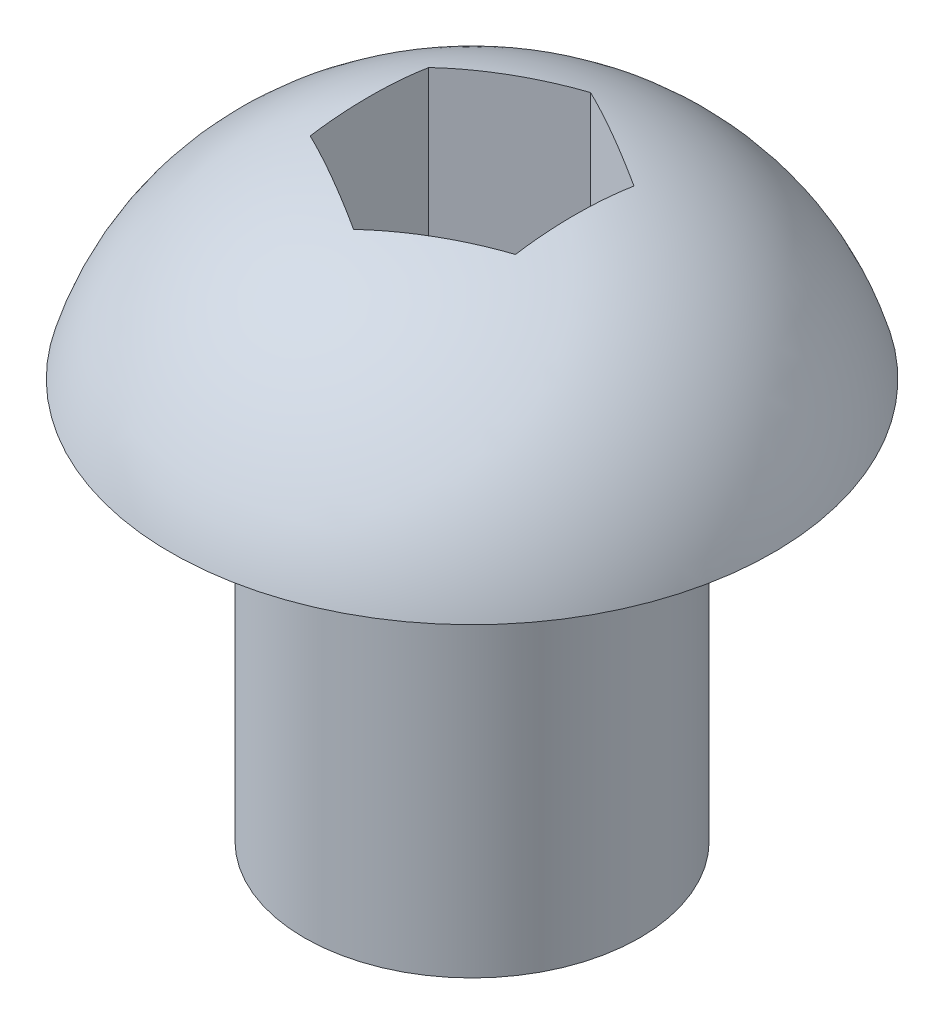
SolidWorks part; units mm, degrees
material "1060 Alloy"
ref_plane "Front Plane" through (0, 0, 0) normal (0, 0, 1) x (1, 0, 0)
ref_plane "Top Plane" through (0, 0, 0) normal (0, 1, 0) x (1, 0, 0)
ref_plane "Right Plane" through (0, 0, 0) normal (1, 0, 0) x (0, 0, -1)
sketch "Sketch1" plane through (0, 0, 0) normal (0, 0, 1) x (1, 0, 0)
  line L0 (0, 0) -> (0, 8.7122)
  line L1 (4.3561, 5.7912) -> (2.4257, 5.7912)
  line L2 (2.4257, 5.7912) -> (2.4257, 0)
  line L3 (2.4257, 0) -> (0, 0)
  line L4 (0, 8.7122) -> (0.4907, 8.7122)
  arc A1 (0.4907, 8.7122) -> (4.3561, 5.7912) centre (0.4907, 4.6942) cw
  dimension "D1" = 8.7122
  dimension "D2" = 5.7912
  dimension "D3" = 1.9304
  dimension "D4" = 2.4257
revolve "Revolve1" add sketch "Sketch1" angle 360 about L0
sketch "Sketch2" plane through (0, 8.7122, 0) normal (0, 1, 0) x (1, 0, 0)
  line L1 (0, -1.7145) -> (1.4848, -0.8572)
  line L2 (1.4848, -0.8572) -> (1.4848, 0.8573)
  line L3 (1.4848, 0.8573) -> (0, 1.7145)
  line L4 (0, 1.7145) -> (-1.4848, 0.8572)
  line L5 (-1.4848, 0.8572) -> (-1.4848, -0.8572)
  line L6 (-1.4848, -0.8572) -> (0, -1.7145)
  circle A0 centre (0, 0) radius 1.4848 construction
  dimension "D1" = 3.429
extrude "Cut-Extrude1" cut sketch "Sketch2" against normal blind 2.54
